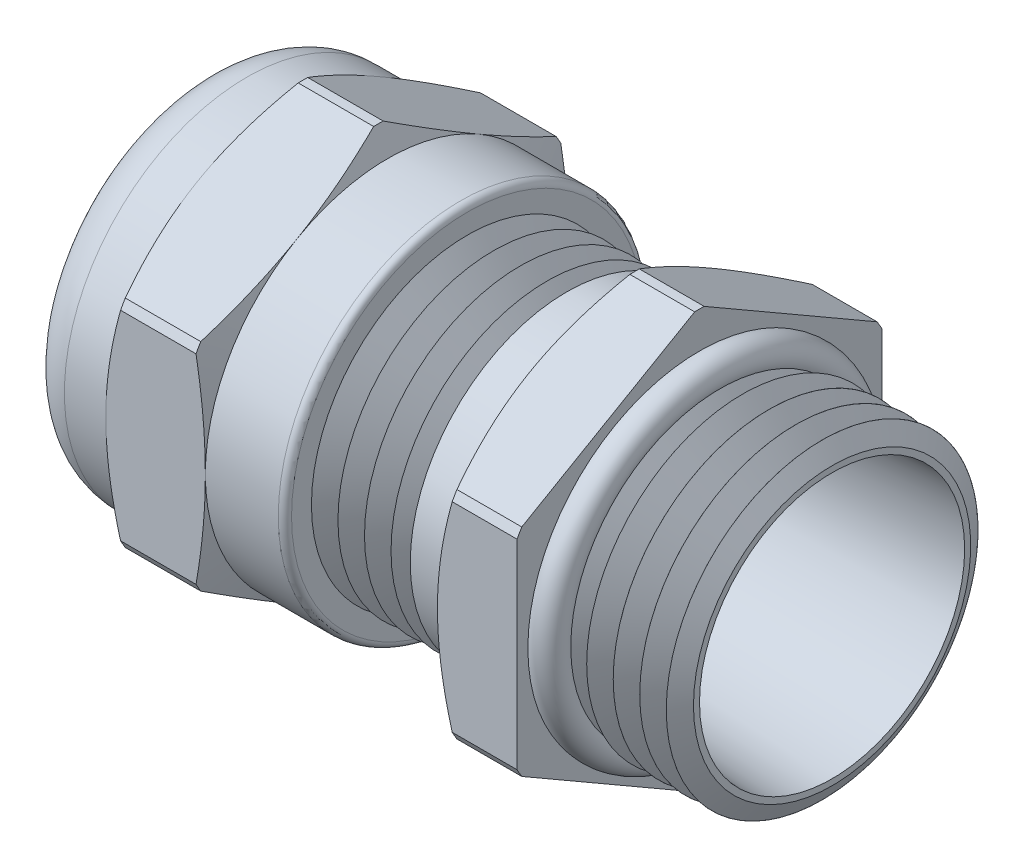
SolidWorks part; units mm, degrees
ref_plane "Front Plane" through (0, 0, 0) normal (0, 0, 1) x (1, 0, 0)
ref_plane "Top Plane" through (0, 0, 0) normal (0, 1, 0) x (1, 0, 0)
ref_plane "Right Plane" through (0, 0, 0) normal (1, 0, 0) x (0, 0, -1)
sketch "Sketch2" plane through (0, 0, 0) normal (0, 0, 1) x (1, 0, 0)
  line L0 (-69.0751, 0) -> (71.6126, 0) construction
  line L1 (-12.065, 5.0641) -> (-12.065, 6.985)
  line L2 (-12.065, 6.985) -> (-8.763, 6.985)
  line L3 (-8.763, 6.985) -> (-8.763, 7.9629)
  line L4 (-8.763, 7.9629) -> (-4.953, 7.9629)
  line L5 (0, 19.614) -> (0, -16.9655) construction
  line L6 (-4.953, 7.9629) -> (-4.953, 6.985)
  line L7 (-4.953, 6.985) -> (-1.905, 6.985)
  line L8 (-1.905, 6.985) -> (-1.905, 5.969)
  line L9 (-1.905, 5.969) -> (3.937, 5.969)
  line L10 (3.937, 5.969) -> (3.937, 7.9629)
  line L11 (3.937, 7.9629) -> (6.985, 7.9629)
  line L12 (6.985, 7.9629) -> (6.985, 5.969)
  line L13 (6.985, 5.969) -> (12.065, 5.9689)
  line L14 (12.065, 5.9689) -> (12.065, 5.0773)
  line L15 (0, 4.445) -> (-8.763, 4.445)
  line L16 (-12.065, 5.0641) -> (-8.763, 5.0641)
  line L17 (-8.763, 5.0641) -> (-8.763, 4.445)
  line L18 (0, 4.445) -> (12.065, 5.0773)
  dimension "D1" = 10.1282
  dimension "CableDia" = 8.89
  dimension "Angle" = 0.001
  dimension "D3" = 3
  dimension "B" = 19.05
  dimension "D" = 5.08
  dimension "NutWidth" = 3.81
  dimension "NutWidth1" = 3.048
  dimension "D4" = 3.302
  dimension "NPT" = 11.938
  dimension "F/F1" = 15.9258
  dimension "D5" = 3.048
  dimension "D6" = 13.97
  dimension "F/F1-" = 13.97
revolve "Revolve1" add sketch "Sketch2" angle 360 about L0
sketch "Sketch6" plane through (6.985, 0, 0) normal (1, 0, 0) x (0, 0, -1)
  line L1 (6.985, -3.8233) -> (6.985, 3.8233)
  line L2 (6.8036, 4.1375) -> (0.1814, 7.9608)
  line L3 (-0.1814, 7.9608) -> (-6.8036, 4.1375)
  line L4 (-6.985, 3.8233) -> (-6.985, -3.8233)
  line L5 (-6.8036, -4.1375) -> (-0.1814, -7.9608)
  line L6 (0.1814, -7.9608) -> (6.8036, -4.1375)
  circle A0 centre (0, 0) radius 6.985 construction
  circle A1 centre (0, 0) radius 7.9629 construction
  arc A2 (6.8036, -4.1375) -> (6.985, -3.8233) centre (0, 0) ccw
  arc A3 (-0.1814, -7.9608) -> (0.1814, -7.9608) centre (0, 0) ccw
  arc A4 (-6.985, -3.8233) -> (-6.8036, -4.1375) centre (0, 0) ccw
  arc A5 (-6.8036, 4.1375) -> (-6.985, 3.8233) centre (0, 0) ccw
  arc A6 (0.1814, 7.9608) -> (-0.1814, 7.9608) centre (0, 0) ccw
  arc A7 (6.985, 3.8233) -> (6.8036, 4.1375) centre (0, 0) ccw
  dimension "F/F1" = 13.97
extrude "Cut-Extrude2" cut sketch "Sketch6" against normal up to surface (15.748 mm away) flip side to cut up to face at (-8.763, 0, 6.985)
sketch "Sketch7" plane through (-8.763, 0, 0) normal (-1, 0, 0) x (0, 0, 1)
  line L0 (-6.985, 3.8233) -> (-6.985, 0) construction
  circle A0 centre (0, 0) radius 6.985
  dimension "D1" = 13.97
extrude "Cut-Extrude3" cut sketch "Sketch7" against normal blind 2.54 draft 60 flip side to cut
sketch "Sketch8" plane through (-4.953, 0, 0) normal (1, 0, 0) x (0, 0, -1)
  line L0 (6.985, 3.8233) -> (6.985, 0) construction
  circle A0 centre (0, 0) radius 6.985
extrude "Cut-Extrude4" cut sketch "Sketch8" against normal blind 2.54 draft 70 flip side to cut
sketch "Sketch9" plane through (3.937, 0, 0) normal (-1, 0, 0) x (0, 0, 1)
  line L0 (-0.1814, -7.9608) -> (-6.8036, -4.1375) construction
  circle A0 centre (0, 0) radius 6.985
extrude "Cut-Extrude5" cut sketch "Sketch9" against normal through all draft 60 flip side to cut
sketch "Sketch12" plane through (0, 0, 0) normal (0, 0, 1) x (1, 0, 0)
  line L0 (-8.763, 4.445) -> (-8.763, 5.0641)
  line L2 (0, 4.445) -> (-8.763, 4.445) construction
  line L3 (-8.763, 5.0641) -> (-11.303, 5.0641)
  line L4 (-8.763, 0) -> (-8.763, 6.0492) construction
  line L5 (-11.557, 4.8101) -> (-11.557, 4.445)
  line L6 (-11.557, 4.445) -> (-8.763, 4.445)
  line L8 (13.8496, 0) -> (-17.3538, 0) construction
  line L9 (-8.763, 5.0641) -> (-12.065, 5.0641) construction
  line L10 (-12.065, 5.0641) -> (-12.065, -5.0641) construction
  arc A0 (-11.303, 5.0641) -> (-11.557, 4.8101) centre (-11.303, 4.8101) ccw
  dimension "D2" = 0.254
  dimension "D1" = 0.508
revolve "Revolve3" add sketch "Sketch12" angle 360 about L8
sketch "Sketch19" [suppressed] plane through (0, 0, 0) normal (0, 0, 1) x (1, 0, 0)
  line L0 (-10.9093, 8.001) -> (-10.9093, 10.8648)
  line L1 (-10.9093, 10.8648) -> (-14.6685, 10.8648)
  line L2 (-10.9093, 10.8648) -> (-15.367, 10.8648) construction
  line L3 (-15.0495, 10.4838) -> (-15.0495, 8.001)
  line L4 (-15.0495, 8.001) -> (-10.9093, 8.001)
  line L5 (-15.367, 14.986) -> (-15.367, -14.986) construction
  line L6 (-10.9093, 0) -> (-10.9093, 12.9783) construction
  line L8 (-17.0501, 0) -> (8.8956, 0) construction
  line L9 (0, 8.001) -> (-10.9093, 8.001) construction
  arc A0 (-14.6685, 10.8648) -> (-15.0495, 10.4838) centre (-14.6685, 10.4838) ccw
  dimension "D2" = 0.381
  dimension "D1" = 0.3175
revolve "Revolve5" [suppressed] add sketch "Sketch19" angle 360 about L8
fillet "Fillet1" radius 1.7145 1 edges at (-12.065, 0, 6.985)
sketch "Sketch13" plane through (0, 0, 0) normal (0, 0, 1) x (1, 0, 0)
  line L0 (-1.905, 5.969) -> (-0.889, 5.969)
  line L1 (-1.905, -6.985) -> (-1.905, 6.985) construction
  line L2 (3.937, 5.969) -> (-1.905, 5.969) construction
  line L3 (-0.889, 5.969) -> (-1.397, 5.0891)
  line L4 (-1.397, 5.0891) -> (-1.905, 5.969)
  line L5 (-15.434, 0) -> (16.1616, 0) construction
  line L6 (-1.397, 5.9839) -> (-1.397, 5.0891) construction
  dimension "D1" = 60
  dimension "P" = 1.016
revolve "Cut-Revolve1" cut sketch "Sketch13" angle 360 about L5
pattern_linear "LPattern1" count 6 spacing 1.016 along (1, 0, 0) of "Cut-Revolve1"
sketch "Sketch14" plane through (0, 0, 0) normal (0, 0, 1) x (1, 0, 0)
  line L0 (7.62, 5.969) -> (8.636, 5.969)
  line L1 (12.065, 5.9689) -> (6.985, 5.969) construction
  line L2 (8.636, 5.969) -> (8.128, 5.0891)
  line L3 (8.128, 5.0891) -> (7.62, 5.969)
  line L5 (-13.7951, 0) -> (13.7951, 0) construction
  line L6 (12.065, 5.9689) -> (6.985, 5.969) construction
  line L7 (6.985, 7.9608) -> (6.985, 4.1375) construction
  line L8 (8.128, 5.0891) -> (8.128, 5.969) construction
  dimension "D1" = 0.635
  dimension "D3" = 60
  dimension "P" = 1.016
revolve "Cut-Revolve2" cut sketch "Sketch14" angle 360 about L5
pattern_linear "LPattern2" count 5 spacing 1.016 along (1, 0, 0) of "Cut-Revolve2"
sketch "Sketch16" plane through (3.937, 0, 0) normal (-1, 0, 0) x (0, 0, 1)
  circle A0 centre (0, 0) radius 5.969 construction
  circle A1 centre (0, 0) radius 5.969 construction
  circle A2 centre (0, 0) radius 5.0773 construction
  circle A3 centre (0, 0) radius 5.0773
  circle A4 centre (0, 0) radius 5.9944
  dimension "D1" = 0.0254
extrude "Extrude4" add sketch "Sketch16" along normal blind 2.032 from offset 0
fillet "Fillet5" radius 0.254 1 edges at (-1.905, 0, 6.985)
sketch "Sketch18" plane through (0, 0, 0) normal (0, 0, 1) x (1, 0, 0)
  line L1 (7.62, 5.969) -> (6.985, 5.969) construction
  line L2 (6.985, 7.9608) -> (6.985, 4.1375) construction
  line L3 (19.1212, 0) -> (-17.421, 0) construction
  circle A0 centre (7.1882, 5.969) radius 0.635
  dimension "D1" = 1.27
  dimension "D2" = 0.2032
revolve "Revolve4" add sketch "Sketch18" angle 360 about L3
sketch "Sketch17" plane through (0, 0, 0) normal (1, 0, 0) x (0, 0, -1)
  line L0 (0, 4.5969) -> (0, -2.0345) construction
  line L1 (-0.2445, 5.0714) -> (-0.2445, 4.9279)
  line L2 (0.2445, 5.0714) -> (0.2445, 4.9279)
  line L3 (4.2697, 2.7474) -> (4.1454, 2.6757)
  line L4 (4.5142, 2.324) -> (4.3899, 2.2522)
  line L5 (4.5142, -2.324) -> (4.3899, -2.2522)
  line L6 (4.2697, -2.7474) -> (4.1454, -2.6757)
  line L7 (0.2445, -5.0714) -> (0.2445, -4.9279)
  line L8 (-0.2445, -5.0714) -> (-0.2445, -4.9279)
  line L9 (-4.2697, -2.7474) -> (-4.1454, -2.6757)
  line L10 (-4.5142, -2.324) -> (-4.3899, -2.2522)
  line L11 (-4.5142, 2.324) -> (-4.3899, 2.2522)
  line L12 (-4.2697, 2.7474) -> (-4.1454, 2.6757)
  circle A0 centre (0, 0) radius 5.0773 construction
  arc A2 (-4.5142, -2.324) -> (-4.2697, -2.7474) centre (0, 0) ccw
  arc A3 (-4.3899, -2.2522) -> (-4.1454, -2.6757) centre (0, 0) ccw construction
  arc A4 (-4.1454, 2.6757) -> (-4.3899, 2.2522) centre (0, 0) ccw construction
  arc A5 (0.2445, 4.9279) -> (-0.2445, 4.9279) centre (0, 0) ccw construction
  arc A6 (4.3899, 2.2522) -> (4.1454, 2.6757) centre (0, 0) ccw construction
  arc A7 (4.1454, -2.6757) -> (4.3899, -2.2522) centre (0, 0) ccw construction
  arc A8 (-0.2445, -4.9279) -> (0.2445, -4.9279) centre (0, 0) ccw construction
  arc A9 (-4.2697, 2.7474) -> (-4.5142, 2.324) centre (0, 0) ccw
  arc A10 (0.2445, 5.0714) -> (-0.2445, 5.0714) centre (0, 0) ccw
  arc A11 (4.5142, 2.324) -> (4.2697, 2.7474) centre (0, 0) ccw
  arc A12 (4.2697, -2.7474) -> (4.5142, -2.324) centre (0, 0) ccw
  arc A13 (-0.2445, -5.0714) -> (0.2445, -5.0714) centre (0, 0) ccw
  circle A16 centre (0, 0) radius 4.445 construction
  arc A17 (-4.3899, 2.2522) -> (-4.3899, -2.2522) centre (0, 0) ccw
  arc A18 (-0.2445, 4.9279) -> (-4.1454, 2.6757) centre (0, 0) ccw
  arc A19 (4.1454, 2.6757) -> (0.2445, 4.9279) centre (0, 0) ccw
  arc A20 (4.3899, -2.2522) -> (4.3899, 2.2522) centre (0, 0) ccw
  arc A21 (0.2445, -4.9279) -> (4.1454, -2.6757) centre (0, 0) ccw
  arc A22 (-4.1454, -2.6757) -> (-0.2445, -4.9279) centre (0, 0) ccw
  circle A23 centre (0, 0) radius 4.445
  dimension "D2" = 0.4889
  dimension "D1" = 0.4889
equation "\"F/F1-@Sketch2\" = \"D6@Sketch2\""
equation "\"D1@Sketch2\" = \"F/F1-@Sketch2\"*0.725"
equation "\"D2@Sketch17\" = \"CableDia@Sketch2\"*0.055"
equation "\"D1@Sketch17\" = \"D2@Sketch17\""
